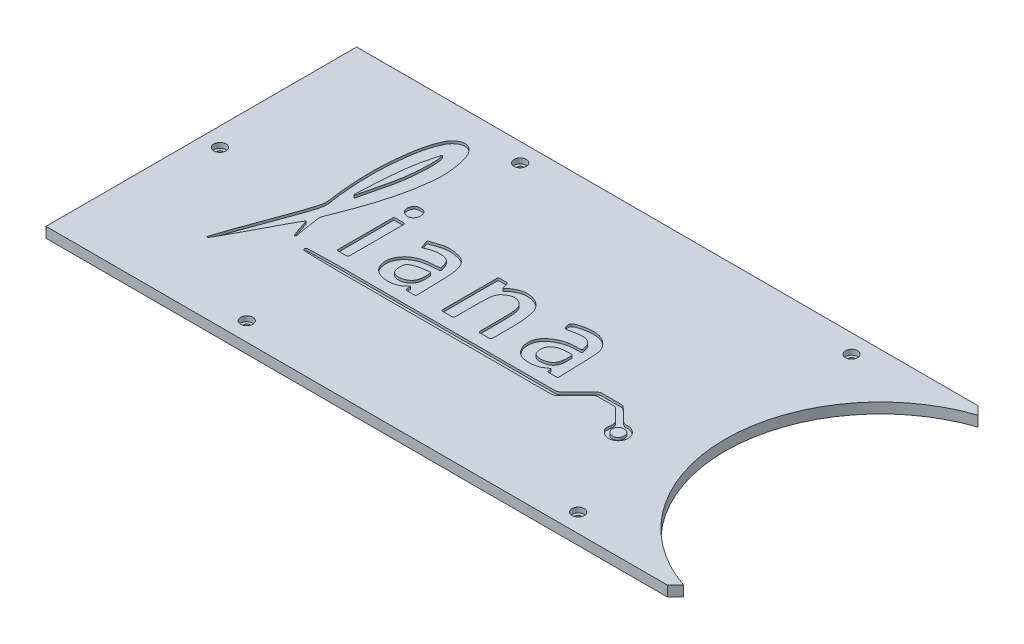
SolidWorks part; units mm, degrees
other "Marca1"
sketch "Croquis4" plane through (-24, 5, 75) normal (0.0144, 0.9293, 0.3691) x (0.9999, -0.0163, 0.0019)
ref_plane "Alzado" through (0, 0, 0) normal (0, 0, 1) x (1, 0, 0)
ref_plane "Planta" through (0, 0, 0) normal (0, 1, 0) x (1, 0, 0)
ref_plane "Vista lateral" through (0, 0, 0) normal (1, 0, 0) x (0, 0, -1)
sketch "Croquis1" plane through (0, 0, 0) normal (0, 1, 0) x (1, 0, 0)
  line L0 (-327.9437, 75) -> (-327.9437, -75)
  line L1 (-327.9437, 75) -> (-27.9437, 75)
  line L2 (-27.9437, 75) -> (-24, 71.0563)
  line L3 (-327.9437, -75) -> (-27.9437, -75)
  line L4 (-27.9437, -75) -> (-24, -71.0563)
  circle A0 centre (0, 0) radius 75 construction
  arc A1 (-24, 71.0563) -> (-24, -71.0563) centre (0, 0) ccw
  point P6 (-327.9437, 0)
  point P11 (-75, 0)
  dimension "D1" = 150
  dimension "D2" = 150
  dimension "D3" = 300
  dimension "D4" = 135
  dimension "D5" = 24
extrude "Saliente-Extruir1" add sketch "Croquis1" along normal blind 5 contours L1 L2 A1 L4 L3 L0
sketch "Croquis2" plane through (0, 5, 0) normal (0, 1, 0) x (1, 0, 0)
  line L0 (-327.9437, 75) -> (-27.9437, 75) construction
  line L1 (-327.9437, -75) -> (-27.9437, -75) construction
  line L2 (-327.9437, 75) -> (-327.9437, -75) construction
  circle A0 centre (-318.9437, 0) radius 1.6
  circle A1 centre (-240.0037, 66) radius 1.6
  circle A2 centre (-240.0037, -66) radius 1.6
  circle A3 centre (-80.0037, -66) radius 1.6
  circle A4 centre (-80.0037, 66) radius 1.6
  dimension "D1" = 3.2
  dimension "D2" = 9
  dimension "D3" = 9
  dimension "D4" = 9
  dimension "D5" = 160
  dimension "D6" = 87.94
extrude "Cortar-Extruir1" cut sketch "Croquis2" against normal blind 5
sketch "Croquis3" plane through (0, 5, 0) normal (0, 1, 0) x (1, 0, 0)
  circle A0 centre (-240.0037, -66) radius 2.95
  circle A1 centre (-80.0037, -66) radius 2.95
  circle A2 centre (-80.0037, 66) radius 2.95
  circle A3 centre (-240.0037, 66) radius 2.95
  circle A4 centre (-318.9437, 0) radius 2.95
  dimension "D1" = 5.9
extrude "Cortar-Extruir2" cut sketch "Croquis3" against normal blind 2.5
sketch "Croquis5" plane through (0, 5, 0) normal (0, 1, 0) x (1, 0, 0)
  spline S0 degree 3 number of poles 565 (-264.8912, -10.407) -> (-264.8912, -10.407)
  spline S1 degree 3 number of poles 279 (-262.6484, 48.2089) -> (-262.6484, 48.2089)
  spline S2 degree 3 number of poles 493 (-213.5311, -14.7576) -> (-213.5311, -14.7576)
  spline S3 degree 3 number of poles 157 (-225.2653, -4.52) -> (-225.2653, -4.52)
  spline S4 degree 3 number of poles 343 (-98.8163, -23.8618) -> (-98.8163, -23.8618)
  spline S5 degree 3 number of poles 343 (-189.9262, 10.8546) -> (-189.9262, 10.8546)
  spline S6 degree 3 number of poles 380 (-145.717, -14.6405) -> (-145.717, -14.6405)
  spline S7 degree 3 number of poles 125 (-156.8594, -5.2926) -> (-156.8594, -5.2926)
  spline S8 degree 3 number of poles 123 (-242.4618, 21.9905) -> (-242.4618, 21.9905)
  spline S9 degree 3 poles (-242.3565, -0.9911) (-242.3565, 3.3839) (-242.3565, 7.7589) (-242.3565, 12.1339) (-242.3565, 12.24) (-242.3565, 12.4521) (-242.7133, 12.8089) (-242.9254, 12.8089) (-243.0315, 12.8089) (-243.7065, 12.8089) (-244.3815, 12.8089) (-245.0565, 12.8089) (-245.7315, 12.8089) (-246.4065, 12.8089) (-247.0815, 12.8089) (-247.1876, 12.8089) (-247.3997, 12.8089) (-247.7565, 12.4521) (-247.7565, 12.24) (-247.7565, 12.1339) (-247.7565, 7.7589) (-247.7565, 3.3839) (-247.7565, -0.9911) (-247.7565, -5.3661) (-247.7565, -9.7411) (-247.7565, -14.1161) (-247.7565, -14.2221) (-247.7565, -14.4343) (-247.3997, -14.7911) (-247.1876, -14.7911) (-247.0815, -14.7911) (-246.4065, -14.7911) (-245.7315, -14.7911) (-245.0565, -14.7911) (-244.3815, -14.7911) (-243.7065, -14.7911) (-243.0315, -14.7911) (-242.9254, -14.7911) (-242.7133, -14.7911) (-242.3565, -14.4343) (-242.3565, -14.2221) (-242.3565, -14.1161) (-242.3565, -9.7411) (-242.3565, -5.3661) (-242.3565, -0.9911) (-242.3565, 3.3839) (-242.3565, 7.7589) knots -0.203746 0 0 0 0.203746 0.203746 0.203746 0.208686 0.213625 0.218565 0.218565 0.218565 0.25 0.25 0.25 0.281435 0.281435 0.281435 0.286375 0.291314 0.296254 0.296254 0.296254 0.5 0.5 0.5 0.703746 0.703746 0.703746 0.708686 0.713625 0.718565 0.718565 0.718565 0.75 0.75 0.75 0.781435 0.781435 0.781435 0.786375 0.791314 0.796254 0.796254 0.796254 1 1 1 1.203746 1.203746 1.203746 only from (-242.3565, -0.9911) to (-242.3565, -0.9911)
  spline S10 degree 3 number of poles 99 (-100.9338, -21.7323) -> (-100.9338, -21.7323)
extrude "Cortar-Extruir3" cut sketch "Croquis5" against normal blind 1.2
